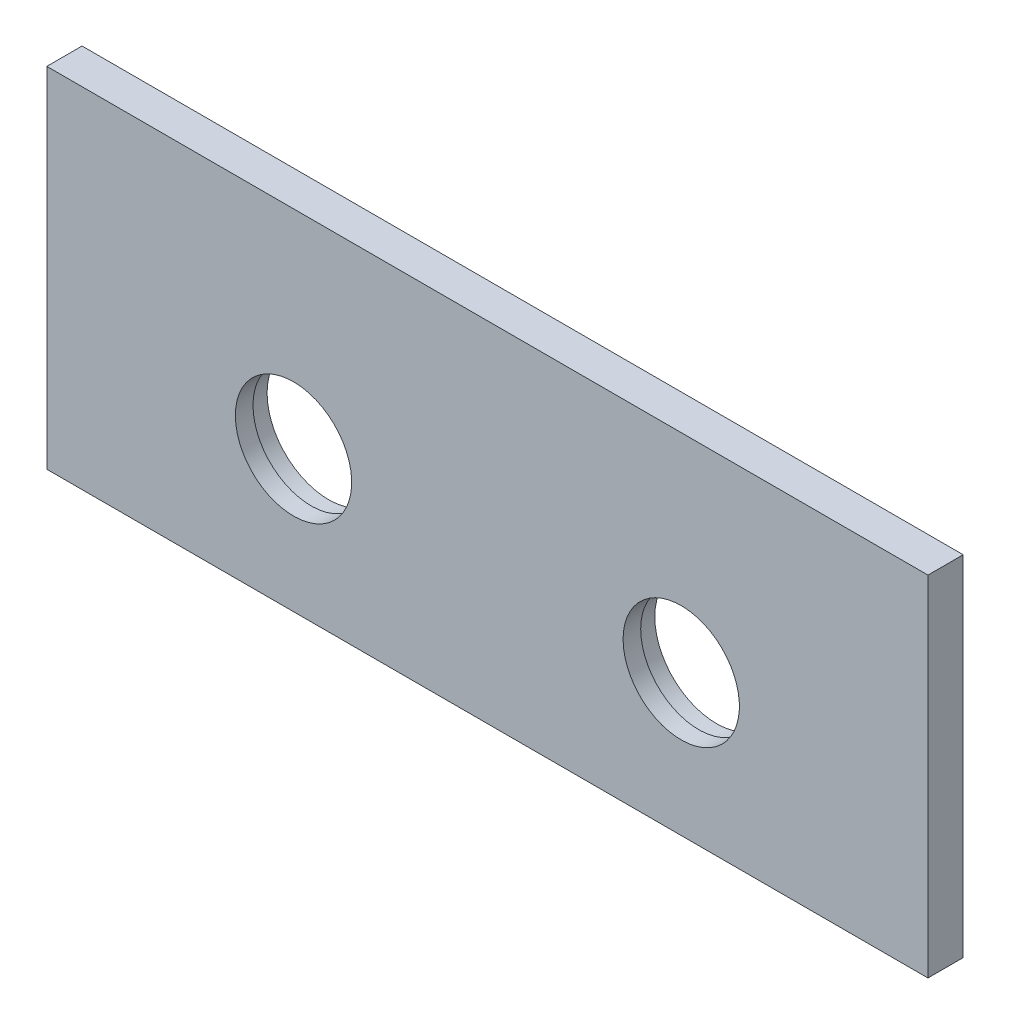
SolidWorks part; units mm, degrees
ref_plane "Front Plane" through (0, 0, 0) normal (0, 0, 1) x (1, 0, 0)
ref_plane "Top Plane" through (0, 0, 0) normal (0, 1, 0) x (1, 0, 0)
ref_plane "Right Plane" through (0, 0, 0) normal (1, 0, 0) x (0, 0, -1)
sketch "Sketch1" plane through (0, 0, 0) normal (0, 0, 1) x (1, 0, 0)
  line L0 (0, -55) -> (0, 55) construction
  line L1 (-125, -49.5) -> (125, -49.5)
  line L2 (-125, -49.5) -> (-125, 49.5)
  line L3 (-125, 49.5) -> (125, 49.5)
  line L4 (125, -49.5) -> (125, 49.5)
  line L5 (0, 38.305) -> (0, 0) construction
  line L6 (0, 0) -> (49.2765, 0) construction
  line L7 (55, 0) -> (-55, 0) construction
  dimension "D1" = 99
  dimension "D2" = 250
extrude "Boss-Extrude1" add sketch "Sketch1" along normal blind 10
hole_wizard "CBORE for M5 Hex Head Bolt1" positions "Sketch3" profile "Sketch2" counterbore size "M5" standard "DIN" end condition through all
sketch "Sketch3" plane through (0, 0, 0) normal (0, 0, -1) x (-1, 0, 0)
  line L0 (0, 5.5) -> (0, -5.5) construction
  line L1 (125, -49.5) -> (-125, -49.5) construction
  point P0 (-55, -9.5)
  dimension "D1" = 55
  dimension "D2" = 40
sketch "Sketch2" plane through (55, -9.5, 0) normal (1, 0, 0) x (0, 1, 0)
  line L0 (0, 0) -> (0, 10)
  line L1 (0, 10) -> (16.5, 10)
  line L3 (16.5, 10) -> (16.5, 5)
  line L4 (16.5, 5) -> (17.5, 5)
  line L5 (17.5, 5) -> (17.5, 0)
  line L7 (17.5, 0) -> (0, 0)
  line L11 (0, -6.35) -> (0, 107.95) construction
  dimension "Thru Hole Dia." = 33
  dimension "Thru Hole Depth" = 10
  dimension "C'Bore Dia." = 35
  dimension "C'Bore Depth" = 5
mirror "Mirror1" about plane through (0, 0, 0) normal (1, 0, 0) of "CBORE for M5 Hex Head Bolt1"
